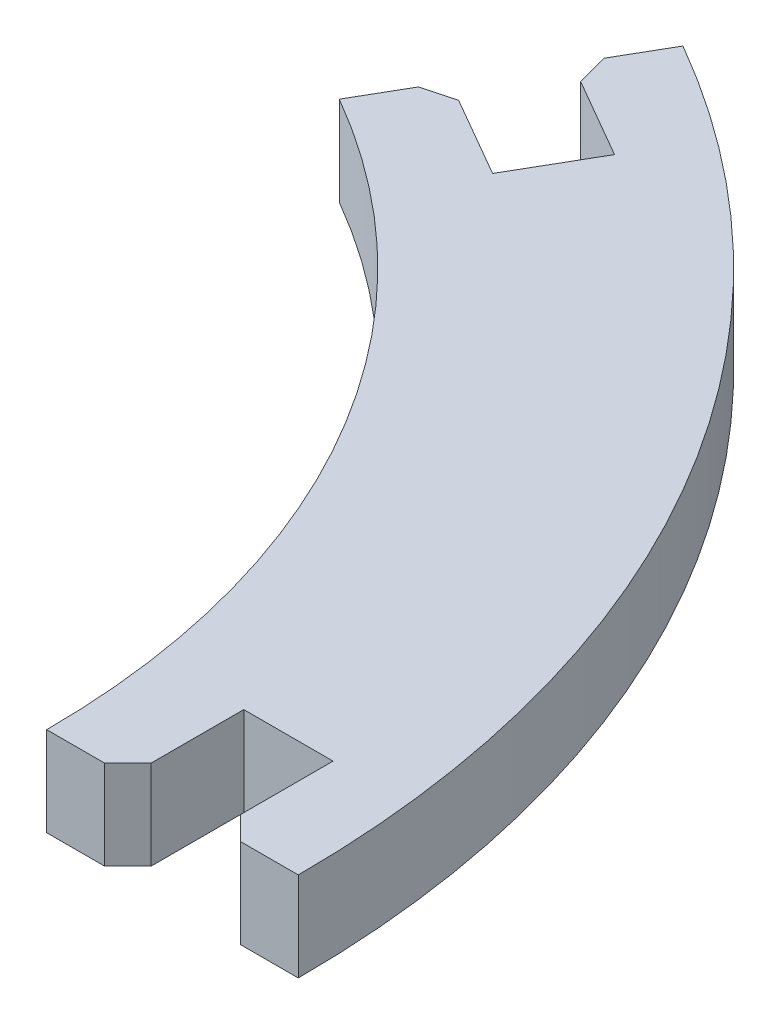
SolidWorks part; units mm, degrees
ref_plane "Front" through (0, 0, 0) normal (0, 0, 1) x (1, 0, 0)
ref_plane "Top" through (0, 0, 0) normal (0, 1, 0) x (1, 0, 0)
ref_plane "Right" through (0, 0, 0) normal (1, 0, 0) x (0, 0, -1)
sketch "Sketch1" plane through (0, 0, 0) normal (0, 1, 0) x (1, 0, 0)
  line L0 (0, 0) -> (83.65, 0) construction
  line L1 (0, 0) -> (27.7517, 48.0673) construction
  line L2 (-12.3899, -7.82) -> (41.0874, -7.82) construction
  line L3 (41.825, 0) -> (41.825, 8.4795) construction
  line L4 (37.975, 0) -> (37.975, 5)
  line L5 (37.975, 5) -> (41.825, 5)
  line L6 (41.825, 5) -> (41.825, 0)
  line L7 (34.475, 0) -> (37.975, 0)
  line L8 (41.825, 0) -> (45.325, 0)
  line L9 (39.9, 5) -> (39.9, -3.7815) construction
  line L10 (0, 0) -> (59.4363, 34.3156) construction
  line L11 (20.9125, 36.2215) -> (22.6625, 39.2526)
  line L12 (23.3176, 30.3873) -> (25.2426, 33.7215)
  line L13 (25.2426, 33.7215) -> (20.9125, 36.2215)
  line L14 (18.9875, 32.8873) -> (23.3176, 30.3873)
  line L15 (17.2375, 29.8562) -> (18.9875, 32.8873)
  line L16 (38.4306, -7.82) -> (41.4306, -7.82) construction
  line L17 (39.9306, -7.82) -> (39.9306, -11.2418) construction
  circle A0 centre (0, 0) radius 41.825 construction
  arc A1 (45.325, 0) -> (22.6625, 39.2526) centre (0, 0) ccw
  arc A2 (34.475, 0) -> (17.2375, 29.8562) centre (0, 0) ccw
  circle A3 centre (-12.3899, -7.82) radius 50.8205 construction
  circle A4 centre (-12.3899, -7.82) radius 53.8205 construction
  circle A5 centre (-12.3899, -7.82) radius 52.3205 construction
  point P25 (38.4306, -7.82)
  dimension "D1" = 60
  dimension "D4" = 5
  dimension "D5" = 3.5
  dimension "D2" = 3.85
  dimension "D3" = 39.9
extrude "Boss-Extrude1" add sketch "Sketch1" along normal blind 3.85 contours A2 L15 L14 L12 L13 L11 A1 L8 L6 L5 L4 L7
chamfer "Chamfer1" distance 1 angle 45 4 edges at (41.825, 1.925, 0) (37.975, 1.925, 0) (18.9875, 1.925, -32.8873) (20.9125, 1.925, -36.2215)
equation "\"entrance\"=5"
equation "\"D4@Sketch1\"=\"entrance\""
equation "\"D2@Sketch1\" = \"thick\""
equation "\"D1@Boss-Extrude1\" = \"thick\""
equation "\"thick\"=3.85"
